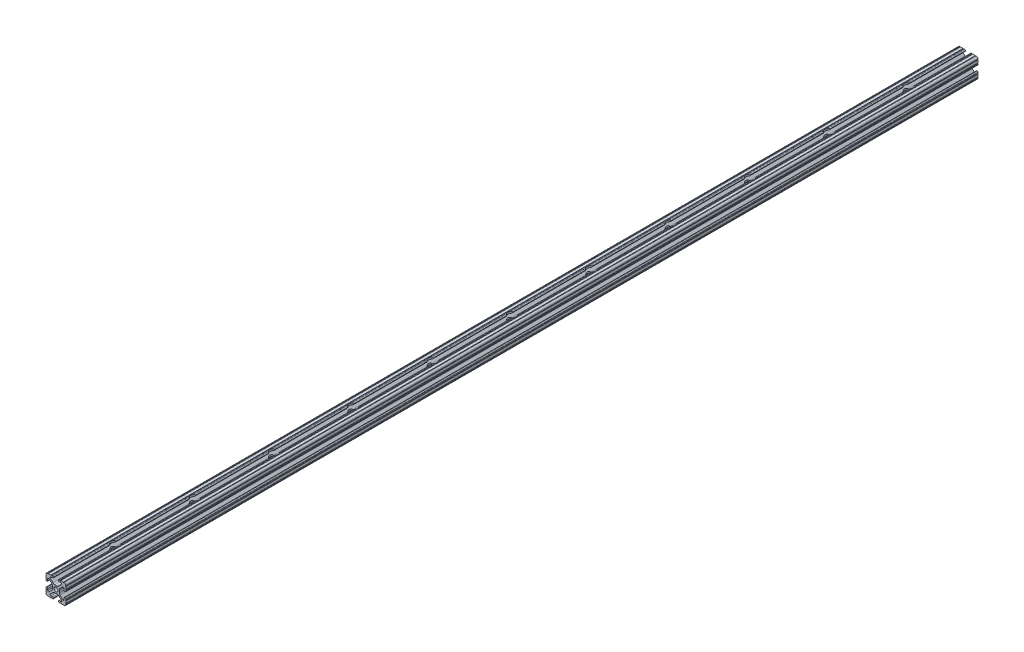
SolidWorks part; units mm, degrees
material "6061-T6 (SS)"
ref_plane "Front Plane" through (0, 0, 0) normal (0, 0, 1) x (1, 0, 0)
ref_plane "Top Plane" through (0, 0, 0) normal (0, 1, 0) x (1, 0, 0)
ref_plane "Right Plane" through (0, 0, 0) normal (1, 0, 0) x (0, 0, -1)
sketch "Sketch1" plane through (0, 0, 0) normal (0, 0, 1) x (1, 0, 0)
  line L0 (-7.207, 8.7244) -> (-3.8983, 5.4232)
  line L1 (-4.2875, 10.4902) -> (-6.4768, 10.4902)
  line L2 (-3.2385, 11.651) -> (-3.2385, 11.5392)
  line L3 (-5.3171, 12.7) -> (-4.2875, 12.7)
  line L4 (0, 13.4005) -> (0, -14.8534) construction
  line L5 (12.7, 0) -> (-13.9989, 0) construction
  line L6 (-9.5504, 12.7) -> (-6.3331, 12.7)
  line L7 (-12.7, 6.3331) -> (-12.7, 9.5504)
  line L8 (-12.7, 4.2875) -> (-12.7, 5.3171)
  line L9 (-11.5392, 3.2385) -> (-11.651, 3.2385)
  line L10 (-10.4902, 6.4021) -> (-10.4902, 4.2875)
  line L11 (-5.441, 3.8408) -> (-8.7371, 7.1294)
  line L12 (-4.5085, -1.5932) -> (-4.5085, 1.5932)
  line L13 (-1.7093, -4.4958) -> (1.7093, -4.4958)
  line L14 (3.9523, -5.4237) -> (7.1797, -8.6452)
  line L15 (6.4164, -10.4902) -> (4.2875, -10.4902)
  line L16 (3.2385, -11.5392) -> (3.2385, -11.651)
  line L17 (4.2875, -12.7) -> (5.3171, -12.7)
  line L18 (6.3331, -12.7) -> (9.5504, -12.7)
  line L19 (12.7, -9.5504) -> (12.7, -6.3331)
  line L20 (12.7, -5.3171) -> (12.7, -4.2875)
  line L21 (11.651, -3.2385) -> (11.5392, -3.2385)
  line L22 (10.4902, -4.2875) -> (10.4902, -6.4021)
  line L23 (8.7371, -7.1294) -> (5.441, -3.8408)
  line L24 (4.5085, -1.5932) -> (4.5085, 1.5932)
  line L25 (5.441, 3.8408) -> (8.7371, 7.1294)
  line L26 (10.4902, 6.4021) -> (10.4902, 4.2875)
  line L27 (11.5392, 3.2385) -> (11.651, 3.2385)
  line L28 (12.7, 4.2875) -> (12.7, 5.3171)
  line L29 (12.7, 6.3331) -> (12.7, 9.5504)
  line L30 (9.5504, 12.7) -> (6.3331, 12.7)
  line L31 (5.3171, 12.7) -> (4.2875, 12.7)
  line L32 (3.2385, 11.651) -> (3.2385, 11.5392)
  line L33 (4.2875, 10.4902) -> (6.4768, 10.4902)
  line L34 (7.207, 8.7244) -> (3.8983, 5.4232)
  line L35 (1.6558, 4.4958) -> (-1.6558, 4.4958)
  line L36 (-8.7371, -7.1294) -> (-5.441, -3.8408)
  line L37 (-10.4902, -4.2875) -> (-10.4902, -6.4021)
  line L38 (-11.651, -3.2385) -> (-11.5392, -3.2385)
  line L39 (-12.7, -5.3171) -> (-12.7, -4.2875)
  line L40 (-12.7, -9.5504) -> (-12.7, -6.3331)
  line L41 (-6.3331, -12.7) -> (-9.5504, -12.7)
  line L42 (-4.2875, -12.7) -> (-5.3171, -12.7)
  line L43 (-3.2385, -11.5392) -> (-3.2385, -11.651)
  line L44 (-6.4164, -10.4902) -> (-4.2875, -10.4902)
  line L45 (-3.9523, -5.4237) -> (-7.1797, -8.6452)
  arc A0 (-7.207, 8.7244) -> (-6.4768, 10.4902) centre (-6.4768, 9.4563) cw
  arc A1 (-3.2385, 11.5392) -> (-4.2875, 10.4902) centre (-4.2875, 11.5392) cw
  arc A2 (-4.2875, 12.7) -> (-3.2385, 11.651) centre (-4.2875, 11.651) cw
  arc A3 (-5.3171, 12.7) -> (-6.3331, 12.7) centre (-5.8251, 12.7) cw
  arc A4 (-9.5504, 12.7) -> (-10.5664, 12.6998) centre (-10.0584, 12.7) cw
  arc A5 (-12.6998, 10.5664) -> (-10.5664, 12.6998) centre (-10.5918, 10.5918) cw
  arc A6 (-12.6998, 10.5664) -> (-12.7, 9.5504) centre (-12.7, 10.0584) cw
  arc A7 (-12.7, 6.3331) -> (-12.7, 5.3171) centre (-12.7, 5.8251) cw
  arc A8 (-11.651, 3.2385) -> (-12.7, 4.2875) centre (-11.651, 4.2875) cw
  arc A9 (-10.4902, 4.2875) -> (-11.5392, 3.2385) centre (-11.5392, 4.2875) cw
  circle A10 centre (0, 0) radius 2.6035
  arc A11 (-10.4902, 6.4021) -> (-8.7371, 7.1294) centre (-9.4628, 6.4021) cw
  arc A12 (-5.441, 3.8408) -> (-4.5085, 1.5932) centre (-7.6835, 1.5932) cw
  arc A13 (-4.5085, -1.5932) -> (-5.441, -3.8408) centre (-7.6835, -1.5932) cw
  arc A14 (-8.7371, -7.1294) -> (-10.4902, -6.4021) centre (-9.4628, -6.4021) cw
  arc A15 (-1.7093, -4.4958) -> (-3.9523, -5.4237) centre (-1.7093, -7.6708) ccw
  arc A16 (3.9523, -5.4237) -> (1.7093, -4.4958) centre (1.7093, -7.6708) ccw
  arc A17 (6.4164, -10.4902) -> (7.1797, -8.6452) centre (6.4164, -9.4098) ccw
  arc A18 (4.2875, -10.4902) -> (3.2385, -11.5392) centre (4.2875, -11.5392) ccw
  arc A19 (3.2385, -11.651) -> (4.2875, -12.7) centre (4.2875, -11.651) ccw
  arc A20 (6.3331, -12.7) -> (5.3171, -12.7) centre (5.8251, -12.7) ccw
  arc A21 (10.5664, -12.6998) -> (9.5504, -12.7) centre (10.0584, -12.7) ccw
  arc A22 (10.5664, -12.6998) -> (12.6998, -10.5664) centre (10.5918, -10.5918) ccw
  arc A23 (12.7, -9.5504) -> (12.6998, -10.5664) centre (12.7, -10.0584) ccw
  arc A24 (12.7, -5.3171) -> (12.7, -6.3331) centre (12.7, -5.8251) ccw
  arc A25 (12.7, -4.2875) -> (11.651, -3.2385) centre (11.651, -4.2875) ccw
  arc A26 (11.5392, -3.2385) -> (10.4902, -4.2875) centre (11.5392, -4.2875) ccw
  arc A27 (8.7371, -7.1294) -> (10.4902, -6.4021) centre (9.4628, -6.4021) ccw
  arc A28 (4.5085, -1.5932) -> (5.441, -3.8408) centre (7.6835, -1.5932) ccw
  arc A29 (5.441, 3.8408) -> (4.5085, 1.5932) centre (7.6835, 1.5932) ccw
  arc A30 (10.4902, 6.4021) -> (8.7371, 7.1294) centre (9.4628, 6.4021) ccw
  arc A31 (10.4902, 4.2875) -> (11.5392, 3.2385) centre (11.5392, 4.2875) ccw
  arc A32 (11.651, 3.2385) -> (12.7, 4.2875) centre (11.651, 4.2875) ccw
  arc A33 (12.7, 6.3331) -> (12.7, 5.3171) centre (12.7, 5.8251) ccw
  arc A34 (12.6998, 10.5664) -> (12.7, 9.5504) centre (12.7, 10.0584) ccw
  arc A35 (12.6998, 10.5664) -> (10.5664, 12.6998) centre (10.5918, 10.5918) ccw
  arc A36 (9.5504, 12.7) -> (10.5664, 12.6998) centre (10.0584, 12.7) ccw
  arc A37 (5.3171, 12.7) -> (6.3331, 12.7) centre (5.8251, 12.7) ccw
  arc A38 (4.2875, 12.7) -> (3.2385, 11.651) centre (4.2875, 11.651) ccw
  arc A39 (3.2385, 11.5392) -> (4.2875, 10.4902) centre (4.2875, 11.5392) ccw
  arc A40 (7.207, 8.7244) -> (6.4768, 10.4902) centre (6.4768, 9.4563) ccw
  arc A41 (1.6558, 4.4958) -> (3.8983, 5.4232) centre (1.6558, 7.6708) ccw
  arc A42 (-1.6558, 4.4958) -> (-3.8983, 5.4232) centre (-1.6558, 7.6708) cw
  arc A43 (-11.5392, -3.2385) -> (-10.4902, -4.2875) centre (-11.5392, -4.2875) cw
  arc A44 (-12.7, -4.2875) -> (-11.651, -3.2385) centre (-11.651, -4.2875) cw
  arc A45 (-12.7, -5.3171) -> (-12.7, -6.3331) centre (-12.7, -5.8251) cw
  arc A46 (-12.7, -9.5504) -> (-12.6998, -10.5664) centre (-12.7, -10.0584) cw
  arc A47 (-10.5664, -12.6998) -> (-12.6998, -10.5664) centre (-10.5918, -10.5918) cw
  arc A48 (-10.5664, -12.6998) -> (-9.5504, -12.7) centre (-10.0584, -12.7) cw
  arc A49 (-6.3331, -12.7) -> (-5.3171, -12.7) centre (-5.8251, -12.7) cw
  arc A50 (-3.2385, -11.651) -> (-4.2875, -12.7) centre (-4.2875, -11.651) cw
  arc A51 (-4.2875, -10.4902) -> (-3.2385, -11.5392) centre (-4.2875, -11.5392) cw
  arc A52 (-6.4164, -10.4902) -> (-7.1797, -8.6452) centre (-6.4164, -9.4098) cw
  dimension "D1" = 5.207
  dimension "D9" = 14.859
  dimension "D2" = 25.4
  dimension "D3" = 12.7
  dimension "D4" = 6.477
  dimension "D5" = 8.2042
  dimension "D6" = 9.017
  dimension "D8" = 2.2098
  dimension "D10" = 2.2098
extrude "Extrude1" add sketch "Sketch1" against normal blind 1168.4
hole_wizard "Hole1, 8020 No. 7256" positions "Sketch3" profile "Sketch2" legacy end condition through all
sketch "Sketch3" plane through (0, 12.7, 0) normal (0, 1, 0) x (1, 0, 0)
  line L0 (0, 0) -> (0, 76.2) construction
  line L1 (1.6558, 0) -> (-1.6558, 0) construction
  point P0 (0, 76.2)
  dimension "D1" = 76.2
sketch "Sketch2" plane through (0, 12.7, -76.2) normal (1, 0, 0) x (0, 0, 1)
  line L0 (0, 0) -> (0, 27.3611)
  line L1 (0, 27.3611) -> (3.2639, 25.4)
  line L2 (3.2639, 25.4) -> (3.2639, 8.255)
  line L3 (3.2639, 8.255) -> (5.1562, 8.255)
  line L4 (5.1562, 0) -> (0, 0)
  line L5 (0, -11.3109) -> (0, 121.1557) construction
  line L6 (0, 27.3611) -> (-3.2639, 25.4) construction
  line L7 (5.1562, 8.255) -> (5.1562, 0)
  dimension "Depth" = 25.4
  dimension "Drill Angle" = 118
  dimension "Diameter" = 6.5278
  dimension "C-Bore Diameter" = 10.3124
  dimension "C-Bore Depth" = 8.255
pattern_linear "LPattern1" count 11 spacing 101.6 along (0, 0, -1) of "Hole1, 8020 No. 7256"
ref_plane "mid plane" through (0, 0, -584.2) normal (0, 0, 1) x (1, 0, 0)
sketch "Sketch4" plane through (0, 0, 0) normal (0, 1, 0) x (1, 0, 0)
  line L1 (-25.4, 1168.4) -> (25.4, 1168.4)
  line L2 (-25.4, 1168.4) -> (-25.4, 279.4)
  line L3 (-25.4, 279.4) -> (25.4, 279.4)
  line L4 (25.4, 1168.4) -> (25.4, 279.4)
  line L6 (25.4, 0) -> (-25.4, 0)
  line L7 (25.4, 0) -> (25.4, 25.4)
  line L8 (25.4, 25.4) -> (-25.4, 25.4)
  line L9 (-25.4, 0) -> (-25.4, 25.4)
  dimension "D1" = 254
  dimension "D2" = 25.4
  dimension "D3" = 50.8
extrude "Cut-Extrude1" [suppressed] cut sketch "Sketch4" against normal through all and the other way through all
